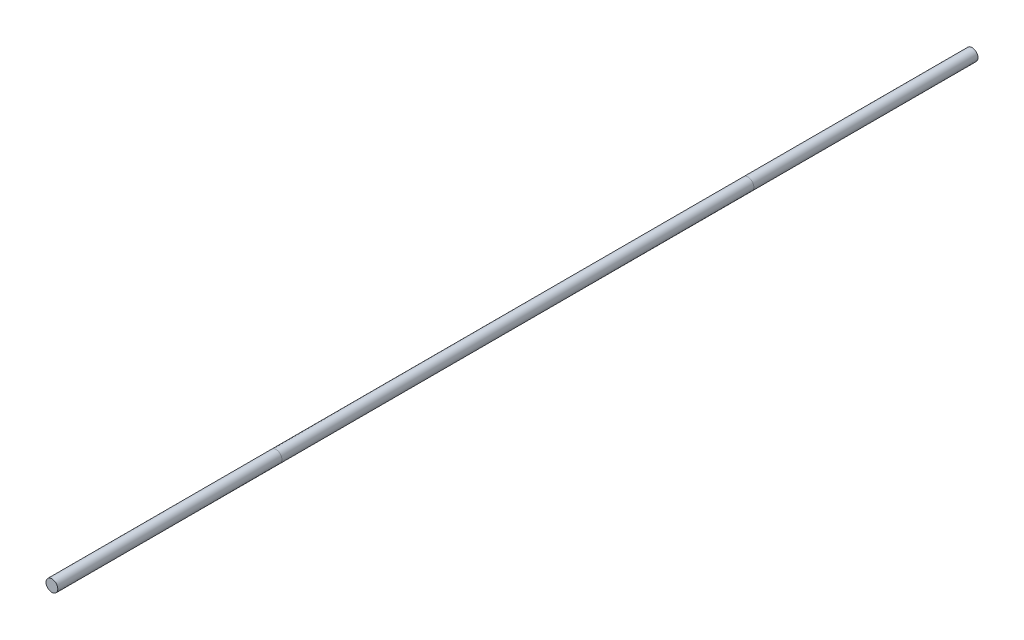
SolidWorks part; units mm, degrees
material "Galvanized Steel"
ref_plane "Front" through (0, 0, 0) normal (0, 0, 1) x (1, 0, 0)
ref_plane "Top" through (0, 0, 0) normal (0, 1, 0) x (1, 0, 0)
ref_plane "Right" through (0, 0, 0) normal (1, 0, 0) x (0, 0, -1)
sketch "Sketch1" plane through (0, 0, 0) normal (0, 0, 1) x (1, 0, 0)
  circle A2 centre (0, 0) radius 3.175
  dimension "D1" = 6.35
extrude "Base-Extrude" add sketch "Sketch1" along normal mid plane 495.3
ref_plane "Plane1" through (0, 0, -127) normal (0, 0, 1) x (1, 0, 0)
ref_plane "Plane2" through (0, 0, 127) normal (0, 0, 1) x (1, 0, 0)
split line "Split Line1"
